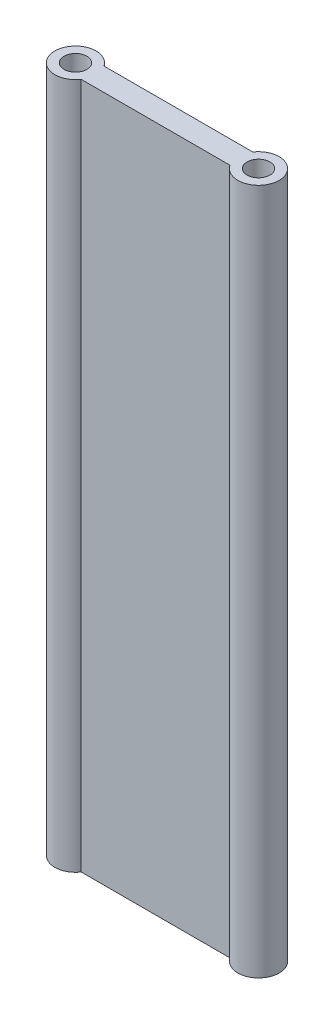
SolidWorks part; units mm, degrees
ref_plane "Front Plane" through (0, 0, 0) normal (0, 0, 1) x (1, 0, 0)
ref_plane "Top Plane" through (0, 0, 0) normal (0, 1, 0) x (1, 0, 0)
ref_plane "Right Plane" through (0, 0, 0) normal (1, 0, 0) x (0, 0, -1)
sketch "Sketch1" plane through (0, 0, 0) normal (0, 1, 0) x (1, 0, 0)
  line L1 (-25.4, -3.175) -> (25.4, -3.175)
  line L2 (-25.4, -3.175) -> (-25.4, 3.175) construction
  line L3 (-25.4, 3.175) -> (25.4, 3.175)
  line L4 (25.4, -3.175) -> (25.4, 3.175) construction
  line L5 (-25.4, -3.175) -> (25.4, 3.175) construction
  line L6 (-25.4, 3.175) -> (25.4, -3.175) construction
  line L8 (25.4, -5.715) -> (25.4, 5.715)
  line L10 (-25.4, -5.715) -> (-25.4, 5.715)
  line L11 (25.4, -5.715) -> (-25.4, 5.715) construction
  line L12 (25.4, 5.715) -> (-25.4, -5.715) construction
  circle A0 centre (25.4, 0) radius 3.175
  circle A1 centre (-25.4, 0) radius 3.175
  arc A2 (-25.4, 5.715) -> (-25.4, -5.715) centre (-25.4, 0) ccw
  circle A5 centre (-25.4, 0) radius 5.715
  circle A6 centre (25.4, 0) radius 5.715
  point P0 (0, 0)
  point P11 (0, 0)
  dimension "D1" = 6.35
  dimension "D3" = 2.54
  dimension "D4" = 2.54
  dimension "D2" = 50.8
extrude "Boss-Extrude1" add sketch "Sketch1" along normal mid plane 190.5
